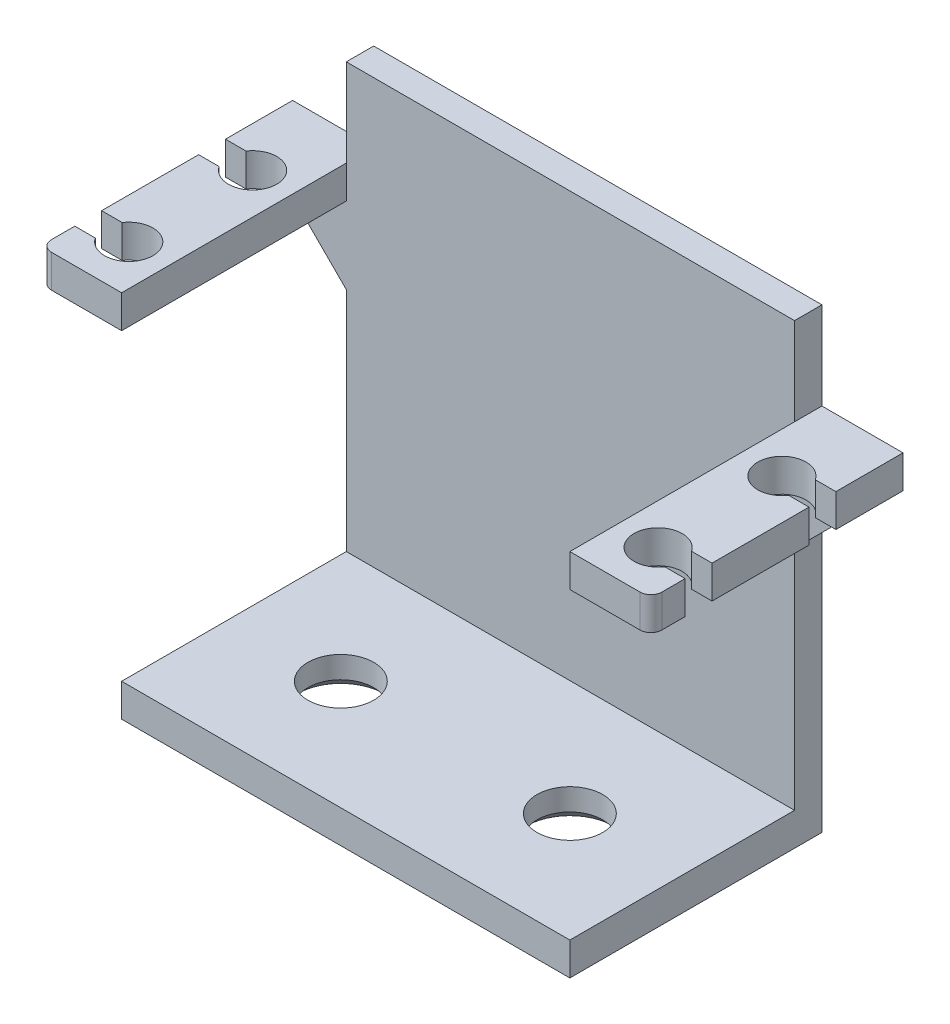
SolidWorks part; units mm, degrees
ref_plane "정면" through (0, 0, 0) normal (0, 0, 1) x (1, 0, 0)
ref_plane "윗면" through (0, 0, 0) normal (0, 1, 0) x (1, 0, 0)
ref_plane "우측면" through (0, 0, 0) normal (1, 0, 0) x (0, 0, -1)
sketch "스케치3" plane through (0, 28.7, 0) normal (0, -1, 0) x (1, 0, 0)
  line L20 (-27.85, -6.875) -> (-27.85, -9)
  line L21 (-26.85, -10) -> (-20.45, -10)
  line L22 (-20.45, -10) -> (-20.45, 10)
  line L23 (-20.45, 10) -> (-26.85, 10)
  line L24 (-27.85, 9) -> (-27.85, 6.875)
  line L25 (-27.85, 6.875) -> (-25.9774, 6.875)
  line L26 (-25.9774, 4.425) -> (-27.85, 4.425)
  line L27 (-27.85, 4.425) -> (-27.85, -4.425)
  line L28 (-27.85, -4.425) -> (-25.9774, -4.425)
  line L29 (-25.9774, -6.875) -> (-27.85, -6.875)
  line L30 (-27.85, -6.875) -> (-27.85, -9)
  line L31 (-27.85, -9) -> (-27.85, -13)
  line L32 (-20.45, -10) -> (-20.45, 10)
  line L33 (-20.45, 10) -> (-26.85, 10)
  line L34 (-27.85, 9) -> (-27.85, 6.875)
  line L35 (-27.85, 6.875) -> (-25.9774, 6.875)
  line L36 (-25.9774, 4.425) -> (-27.85, 4.425)
  line L37 (-27.85, 4.425) -> (-27.85, -4.425)
  line L38 (-27.85, -4.425) -> (-25.9774, -4.425)
  line L39 (-25.9774, -6.875) -> (-27.85, -6.875)
  line L40 (-27.85, -13) -> (27.85, -13)
  line L41 (27.85, -13) -> (27.85, -9)
  line L42 (-20.45, -10) -> (-20.45, -10.5)
  line L43 (-20.45, -10.5) -> (20.45, -10.5)
  line L44 (20.45, -10.5) -> (20.45, -10)
  line L45 (20.45, -10) -> (-20.45, -10) construction
  line L50 (20.45, -10) -> (26.85, -10)
  line L51 (27.85, -9) -> (27.85, -6.875)
  line L52 (27.85, -6.875) -> (25.9774, -6.875)
  line L53 (25.9774, -4.425) -> (27.85, -4.425)
  line L54 (27.85, -4.425) -> (27.85, 4.425)
  line L55 (27.85, 4.425) -> (25.9774, 4.425)
  line L56 (25.9774, 6.875) -> (27.85, 6.875)
  line L57 (27.85, 6.875) -> (27.85, 9)
  line L58 (26.85, 10) -> (20.45, 10)
  line L59 (20.45, 10) -> (20.45, -10)
  line L61 (27.85, -9) -> (27.85, -6.875)
  line L62 (27.85, -6.875) -> (25.9774, -6.875)
  line L63 (25.9774, -4.425) -> (27.85, -4.425)
  line L64 (27.85, -4.425) -> (27.85, 4.425)
  line L65 (27.85, 4.425) -> (25.9774, 4.425)
  line L66 (25.9774, 6.875) -> (27.85, 6.875)
  line L67 (27.85, 6.875) -> (27.85, 9)
  line L68 (26.85, 10) -> (20.45, 10)
  line L69 (20.45, 10) -> (20.45, -10)
  arc A8 (-27.85, -9) -> (-26.85, -10) centre (-26.85, -9) ccw
  arc A9 (-26.85, 10) -> (-27.85, 9) centre (-26.85, 9) ccw
  arc A10 (-25.9774, 4.425) -> (-25.9774, 6.875) centre (-24.15, 5.65) ccw
  arc A11 (-25.9774, -6.875) -> (-25.9774, -4.425) centre (-24.15, -5.65) ccw
  arc A13 (-26.85, 10) -> (-27.85, 9) centre (-26.85, 9) ccw
  arc A14 (-25.9774, 4.425) -> (-25.9774, 6.875) centre (-24.15, 5.65) ccw
  arc A15 (-25.9774, -6.875) -> (-25.9774, -4.425) centre (-24.15, -5.65) ccw
  arc A20 (26.85, -10) -> (27.85, -9) centre (26.85, -9) ccw
  arc A21 (25.9774, -4.425) -> (25.9774, -6.875) centre (24.15, -5.65) ccw
  arc A22 (25.9774, 6.875) -> (25.9774, 4.425) centre (24.15, 5.65) ccw
  arc A23 (27.85, 9) -> (26.85, 10) centre (26.85, 9) ccw
  arc A25 (25.9774, -4.425) -> (25.9774, -6.875) centre (24.15, -5.65) ccw
  arc A26 (25.9774, 6.875) -> (25.9774, 4.425) centre (24.15, 5.65) ccw
  arc A27 (27.85, 9) -> (26.85, 10) centre (26.85, 9) ccw
  dimension "D3" = 0.5
  dimension "D4" = 2.5
  dimension "D1" = 0
  dimension "D2" = 0
extrude "보스-돌출2" add sketch "스케치3" along normal blind 3
sketch "스케치4" plane through (0, 25.7, 0) normal (0, -1, 0) x (1, 0, 0)
  line L0 (-27.85, -13) -> (27.85, -13) construction
  line L1 (-20.45, -10.5) -> (20.45, -10.5)
  line L2 (-20.45, -10.5) -> (-20.45, -13)
  line L3 (-20.45, -13) -> (20.45, -13)
  line L4 (20.45, -10.5) -> (20.45, -13)
extrude "보스-돌출3" add sketch "스케치4" along normal blind 27.7
sketch "스케치5" plane through (0, -2, 0) normal (0, -1, 0) x (1, 0, 0)
  line L1 (-20.45, -13) -> (20.45, -13)
  line L2 (-20.45, -13) -> (-20.45, 10)
  line L3 (-20.45, 10) -> (20.45, 10)
  line L4 (20.45, -13) -> (20.45, 10)
extrude "보스-돌출4" add sketch "스케치5" along normal blind 3
sketch "스케치6" plane through (0, 0, -13) normal (0, 0, -1) x (-1, 0, 0)
  line L1 (-20.45, 10.35) -> (20.45, 10.35) construction
  line L2 (-20.45, -5) -> (-20.45, 25.7) construction
  line L3 (20.45, -5) -> (20.45, 25.7) construction
  line L4 (0, -5) -> (0, 28.7) construction
  line L5 (20.45, -5) -> (-20.45, -5) construction
  line L6 (27.85, 28.7) -> (-27.85, 28.7) construction
  circle A0 centre (-10.45, 3) radius 4
  circle A1 centre (-10.45, 17.7) radius 4
  circle A2 centre (10.45, 3) radius 4
  circle A3 centre (10.45, 17.7) radius 4
  dimension "D1" = 10
  dimension "D3" = 8
  dimension "D2" = 8
chamfer "모따기2" distance 7 2 edges
sketch "스케치8" plane through (0, -5, 0) normal (0, -1, 0) x (1, 0, 0)
  circle A0 centre (10.45, 0) radius 3
  dimension "D1" = 6
extrude "컷-돌출3" cut sketch "스케치8" against normal up to next (3 mm away)
chamfer "모따기3" distance 1 angle 45 1 edges at (10.45, -5, -3)
mirror "대칭 복사1" about plane through (0, 0, 0) normal (1, 0, 0) of "모따기3", "컷-돌출3"
sketch "스케치9" plane through (0, 28.7, 0) normal (0, 1, 0) x (1, 0, 0)
  line L0 (20.45, 10.5) -> (-20.45, 10.5)
  line L1 (20.45, 10.5) -> (20.45, 13)
  line L2 (-20.45, 10.5) -> (-20.45, 13)
  line L3 (20.45, 13) -> (-20.45, 13)
  line L4 (-27.85, 13) -> (27.85, 13) construction
  dimension "D1" = 0
extrude "보스-돌출5" add sketch "스케치9" along normal blind 8
